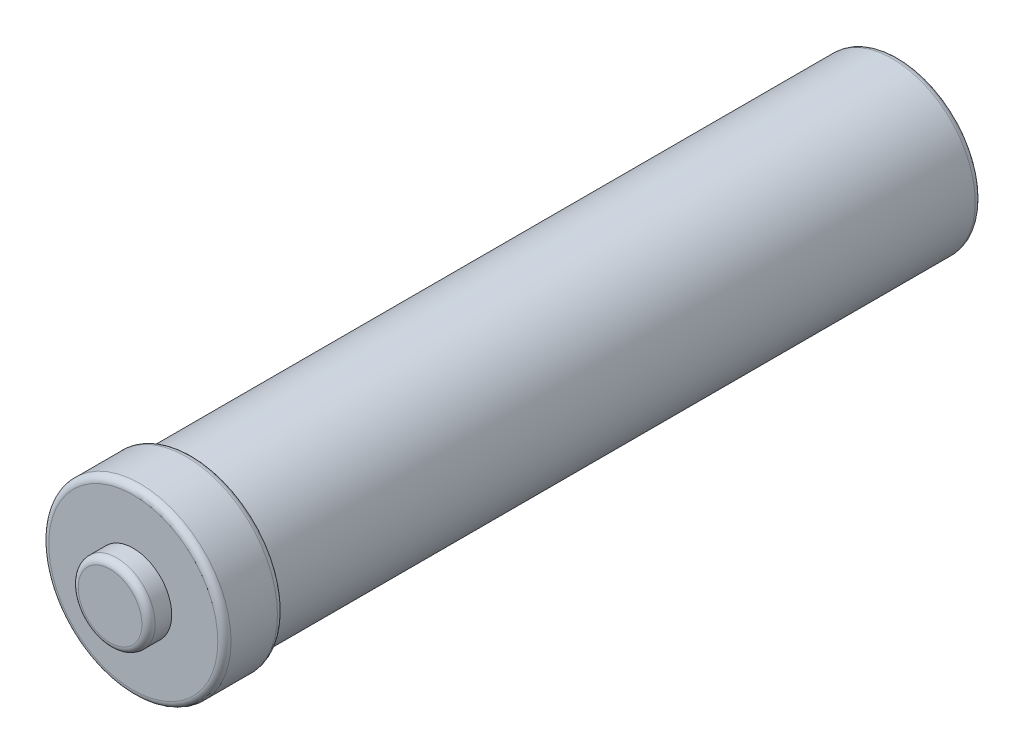
SolidWorks part; units mm, degrees
ref_plane "Front Plane" through (0, 0, 0) normal (0, 0, 1) x (1, 0, 0)
ref_plane "Top Plane" through (0, 0, 0) normal (0, 1, 0) x (1, 0, 0)
ref_plane "Right Plane" through (0, 0, 0) normal (1, 0, 0) x (0, 0, -1)
sketch "Sketch1" plane through (0, 0, 0) normal (0, 0, 1) x (1, 0, 0)
  circle A0 centre (0, 0) radius 14.732
  dimension "D1" = 29.464
extrude "Boss-Extrude1" add sketch "Sketch1" along normal blind 8.89
sketch "Sketch2" plane through (0, 0, 8.89) normal (0, 0, 1) x (1, 0, 0)
  circle A0 centre (0, 0) radius 31.75
  dimension "D1" = 63.5
extrude "Boss-Extrude2" add sketch "Sketch2" along normal blind 270.51
sketch "Sketch3" plane through (0, 0, 279.4) normal (0, 0, 1) x (1, 0, 0)
  circle A0 centre (0, 0) radius 34.925
  dimension "D1" = 69.85
extrude "Boss-Extrude3" add sketch "Sketch3" along normal blind 22.86
ref_plane "Plane1" through (0, 0, 155.575) normal (0, 0, -1) x (-1, 0, 0)
mirror "Mirror1" about plane through (0, 0, 155.575) normal (0, 0, -1) of "Boss-Extrude1"
fillet "Fillet1" radius 2.54 5 edges at (14.732, 0, 0) (31.75, 0, 8.89) (34.925, 0, 279.4) (34.925, 0, 302.26) (14.732, 0, 311.15)
